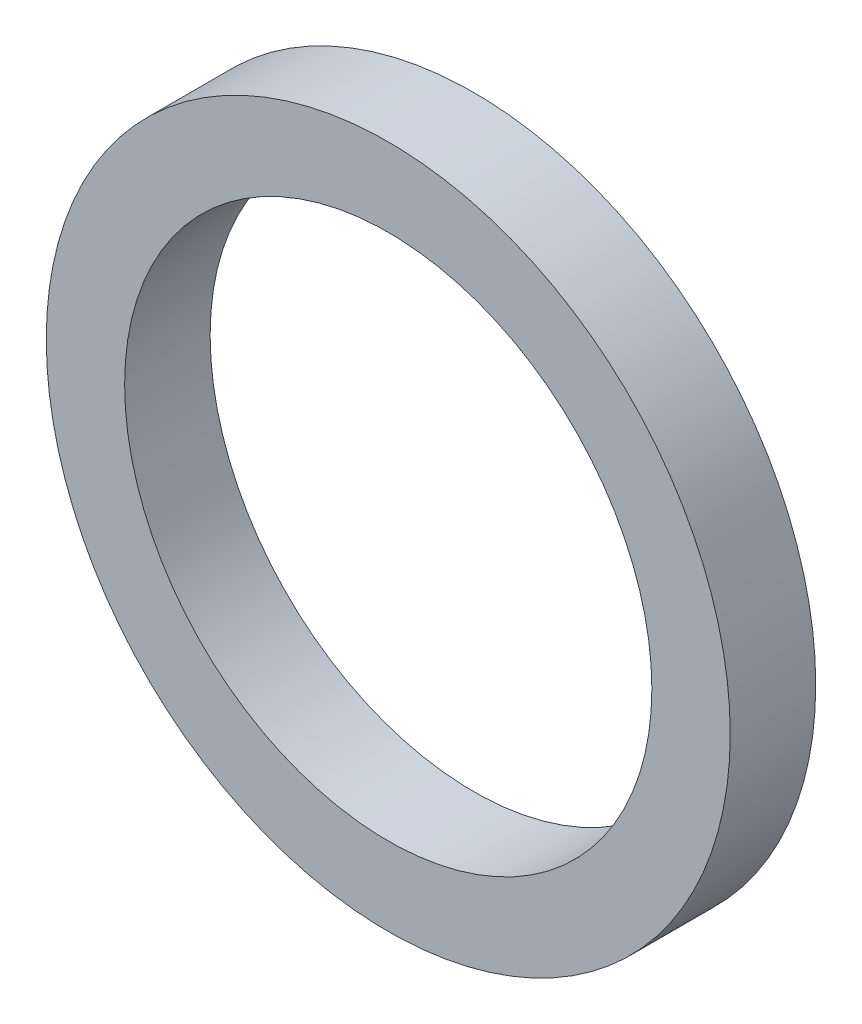
SolidWorks part; units mm, degrees
ref_plane "Front Plane" through (0, 0, 0) normal (0, 0, 1) x (1, 0, 0)
ref_plane "Top Plane" through (0, 0, 0) normal (0, 1, 0) x (1, 0, 0)
ref_plane "Right Plane" through (0, 0, 0) normal (1, 0, 0) x (0, 0, -1)
sketch "Sketch1" plane through (0, 0, 0) normal (0, 0, 1) x (1, 0, 0)
  circle A0 centre (0, 0) radius 12
  circle A1 centre (0, 0) radius 9.25
extrude "Boss-Extrude1" add sketch "Sketch1" along normal blind 3
